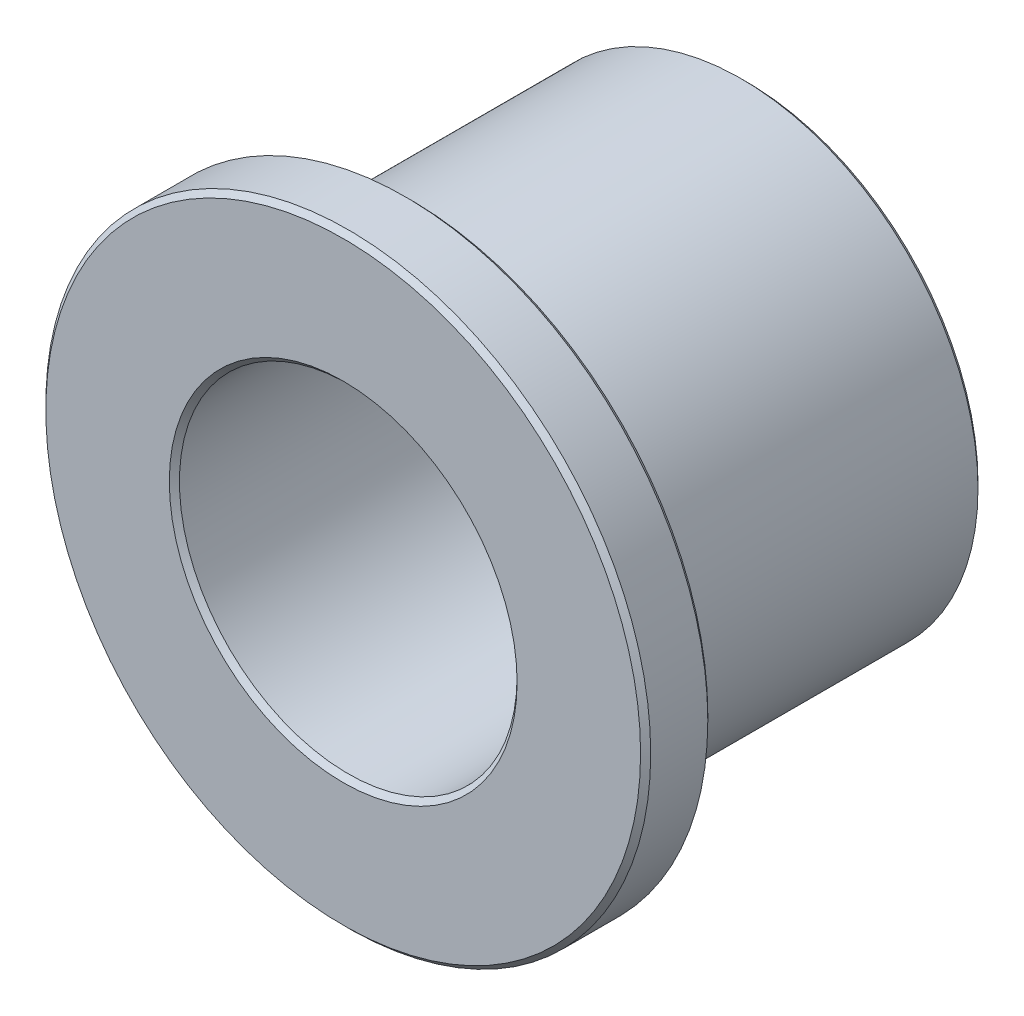
SolidWorks part; units mm, degrees
ref_plane "Front" through (0, 0, 0) normal (0, 0, 1) x (1, 0, 0)
ref_plane "Top" through (0, 0, 0) normal (0, 1, 0) x (1, 0, 0)
ref_plane "Right" through (0, 0, 0) normal (1, 0, 0) x (0, 0, -1)
sketch "Sketch1" plane through (0, 0, 0) normal (0, 0, 1) x (1, 0, 0)
  circle A0 centre (0, 0) radius 3.9878
  circle A1 centre (0, 0) radius 5.588
  circle A2 centre (0, 0) radius 7.1438
  dimension "ID" = 7.9756
  dimension "OD" = 11.176
  dimension "Flange OD" = 14.2875
sketch "Sketch2" plane through (0, 0, 0) normal (1, 0, 0) x (0, 0, -1)
  line L0 (-4.7625, -7.1438) -> (4.7625, -7.1438) construction
  line L1 (0, 7.1438) -> (0, -7.1438) construction
  line L3 (-3.175, 5.588) -> (4.7625, 5.588) construction
  point P3 (0, -7.1438)
  point P7 (0, 5.588)
  point P9 (-3.175, -7.1438)
  point P10 (-4.7625, 7.1438)
  point P23 (0, 7.1438)
  dimension "Flange Thickness" = 1.5875
  dimension "Length" = 9.525
sketch "Sketch3" plane through (0, 0, 0) normal (0, 0, 1) x (1, 0, 0)
  circle A0 centre (0, 0) radius 7.1438 construction
  circle A1 centre (0, 0) radius 7.1438
  circle A2 centre (0, 0) radius 3.9878 construction
  circle A3 centre (0, 0) radius 3.9878
extrude "Boss-Extrude1" add sketch "Sketch3" against normal up to vertex (-3.175 mm away) from vertex at 4.7625 starting at point (0, -7.1438, 4.7625)
sketch "Sketch4" plane through (0, 0, 0) normal (0, 0, 1) x (1, 0, 0)
  circle A0 centre (0, 0) radius 3.9878 construction
  circle A1 centre (0, 0) radius 5.588 construction
  circle A2 centre (0, 0) radius 3.9878
  circle A3 centre (0, 0) radius 5.588
extrude "Boss-Extrude2" add sketch "Sketch4" against normal up to vertex (4.7625 mm away) from vertex at 3.175 starting at point (0, -7.1438, 3.175)
chamfer "Chamfer1" distance 0.1196 angle 45 6 edges at (3.9878, 0, 4.7625) (7.1438, 0, 4.7625) (7.1438, 0, 3.175) (5.588, 0, 3.175) (3.9878, 0, -4.7625) (5.588, 0, -4.7625)
equation "\"D1@Chamfer1\"=\"ID@Sketch1\"*0.015"
